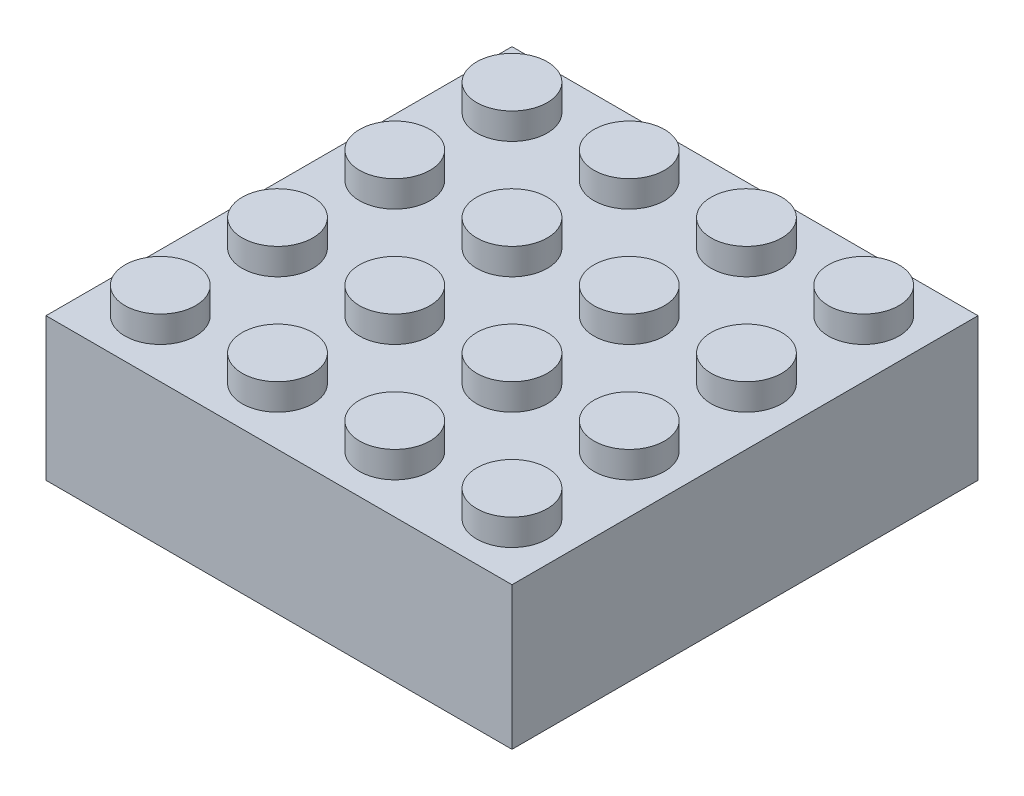
SolidWorks part; units mm, degrees
ref_plane "Front Plane" through (0, 0, 0) normal (0, 0, 1) x (1, 0, 0)
ref_plane "Top Plane" through (0, 0, 0) normal (0, 1, 0) x (1, 0, 0)
ref_plane "Right Plane" through (0, 0, 0) normal (1, 0, 0) x (0, 0, -1)
sketch "Sketch1" plane through (0, 0, 0) normal (0, 1, 0) x (1, 0, 0)
  line L1 (0, 0) -> (31.8, 0)
  line L2 (0, 0) -> (0, 31.8)
  line L3 (0, 31.8) -> (31.8, 31.8)
  line L4 (31.8, 0) -> (31.8, 31.8)
  dimension "D1" = 31.8
  dimension "D2" = 31.8
sketch "Sketch2" plane through (0, 0, 0) normal (0, 1, 0) x (1, 0, 0)
  line L0 (0, 0) -> (0, 31.8) construction
  line L1 (0, 31.8) -> (31.8, 31.8) construction
  circle A0 centre (3.9, 27.9) radius 2.41
  circle A1 centre (11.9, 27.9) radius 2.41
  circle A2 centre (19.9, 27.9) radius 2.41
  circle A3 centre (27.9, 27.9) radius 2.41
  circle A4 centre (11.9, 19.9) radius 2.41
  circle A5 centre (19.9, 19.9) radius 2.41
  circle A6 centre (27.9, 19.9) radius 2.41
  circle A7 centre (11.9, 11.9) radius 2.41
  circle A8 centre (19.9, 11.9) radius 2.41
  circle A9 centre (27.9, 11.9) radius 2.41
  circle A10 centre (11.9, 3.9) radius 2.41
  circle A11 centre (19.9, 3.9) radius 2.41
  circle A12 centre (27.9, 3.9) radius 2.41
  circle A13 centre (3.9, 19.9) radius 2.41
  circle A14 centre (3.9, 11.9) radius 2.41
  circle A15 centre (3.9, 3.9) radius 2.41
  dimension "D3" = 4.82
  dimension "D1" = 3.9
  dimension "D2" = 3.9
  dimension "D4" = 4
  dimension "D5" = 4
extrude "Boss-Extrude1" add sketch "Sketch2" along normal blind 1.8
extrude "Boss-Extrude2" add sketch "Sketch1" against normal blind 9.73
sketch "Sketch4" plane through (0, -9.73, 0) normal (0, -1, 0) x (1, 0, 0)
  line L0 (0.99, 0) -> (-0.99, 0) construction
  line L1 (25.14, -15.9) -> (20.52, -7.8979)
  line L2 (20.52, -7.8979) -> (11.28, -7.8979)
  line L3 (11.28, -7.8979) -> (6.66, -15.9)
  line L4 (6.66, -15.9) -> (11.28, -23.9021)
  line L5 (11.28, -23.9021) -> (20.52, -23.9021)
  line L6 (20.52, -23.9021) -> (25.14, -15.9)
  line L7 (0, -0.99) -> (0, 0.99) construction
  circle A0 centre (15.9, -15.9) radius 8.0021 construction
  dimension "D1" = 15.9
  dimension "D2" = 15.9
  dimension "D3" = 9.24
extrude "Cut-Extrude1" cut sketch "Sketch4" against normal blind 6.63
